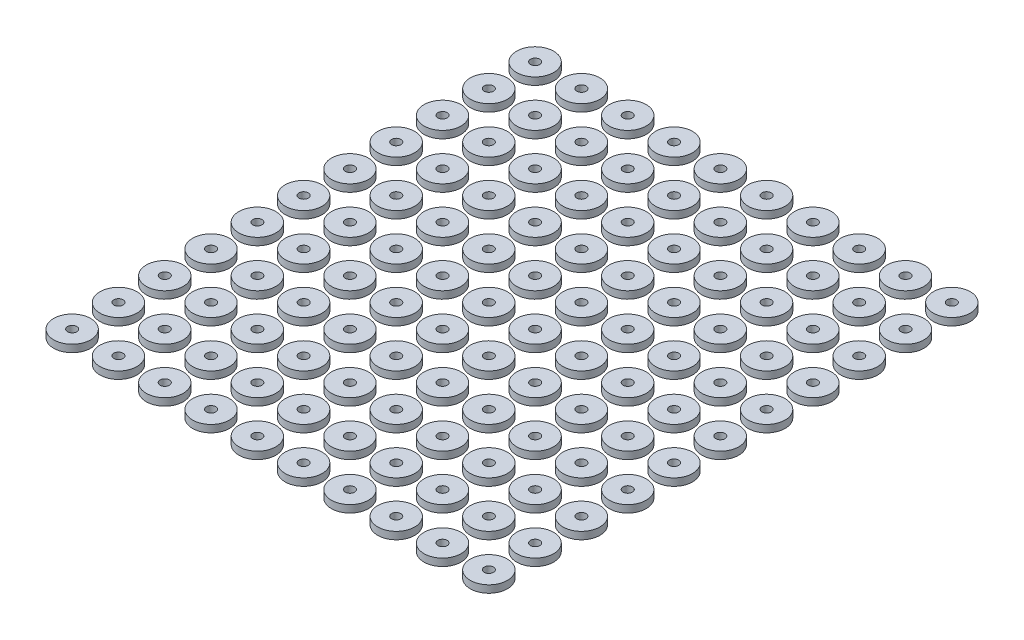
SolidWorks part; units mm, degrees
ref_plane "Front Plane" through (0, 0, 0) normal (0, 0, 1) x (1, 0, 0)
ref_plane "Top Plane" through (0, 0, 0) normal (0, 1, 0) x (1, 0, 0)
ref_plane "Right Plane" through (0, 0, 0) normal (1, 0, 0) x (0, 0, -1)
sketch "Sketch1" plane through (0, 0, 0) normal (0, 1, 0) x (1, 0, 0)
  circle A0 centre (0, 0) radius 4
  circle A110 centre (0, 0) radius 1
  circle A111 centre (10, 0) radius 4
  circle A112 centre (10, 0) radius 1
  circle A113 centre (20, 0) radius 4
  circle A114 centre (20, 0) radius 1
  circle A115 centre (30, 0) radius 4
  circle A116 centre (30, 0) radius 1
  circle A117 centre (40, 0) radius 4
  circle A118 centre (40, 0) radius 1
  circle A119 centre (50, 0) radius 4
  circle A120 centre (50, 0) radius 1
  circle A121 centre (60, 0) radius 4
  circle A122 centre (60, 0) radius 1
  circle A123 centre (70, 0) radius 4
  circle A124 centre (70, 0) radius 1
  circle A125 centre (80, 0) radius 4
  circle A126 centre (80, 0) radius 1
  circle A127 centre (90, 0) radius 4
  circle A128 centre (90, 0) radius 1
  circle A129 centre (10, 10) radius 4
  circle A130 centre (10, 10) radius 1
  circle A131 centre (20, 10) radius 4
  circle A132 centre (20, 10) radius 1
  circle A133 centre (30, 10) radius 4
  circle A134 centre (30, 10) radius 1
  circle A135 centre (40, 10) radius 4
  circle A136 centre (40, 10) radius 1
  circle A137 centre (50, 10) radius 4
  circle A138 centre (50, 10) radius 1
  circle A139 centre (60, 10) radius 4
  circle A140 centre (60, 10) radius 1
  circle A141 centre (70, 10) radius 4
  circle A142 centre (70, 10) radius 1
  circle A143 centre (80, 10) radius 4
  circle A144 centre (80, 10) radius 1
  circle A145 centre (90, 10) radius 4
  circle A146 centre (90, 10) radius 1
  circle A147 centre (10, 20) radius 4
  circle A148 centre (10, 20) radius 1
  circle A149 centre (20, 20) radius 4
  circle A150 centre (20, 20) radius 1
  circle A151 centre (30, 20) radius 4
  circle A152 centre (30, 20) radius 1
  circle A153 centre (40, 20) radius 4
  circle A154 centre (40, 20) radius 1
  circle A155 centre (50, 20) radius 4
  circle A156 centre (50, 20) radius 1
  circle A157 centre (60, 20) radius 4
  circle A158 centre (60, 20) radius 1
  circle A159 centre (70, 20) radius 4
  circle A160 centre (70, 20) radius 1
  circle A161 centre (80, 20) radius 4
  circle A162 centre (80, 20) radius 1
  circle A163 centre (90, 20) radius 4
  circle A164 centre (90, 20) radius 1
  circle A165 centre (10, 30) radius 4
  circle A166 centre (10, 30) radius 1
  circle A167 centre (20, 30) radius 4
  circle A168 centre (20, 30) radius 1
  circle A169 centre (30, 30) radius 4
  circle A170 centre (30, 30) radius 1
  circle A171 centre (40, 30) radius 4
  circle A172 centre (40, 30) radius 1
  circle A173 centre (50, 30) radius 4
  circle A174 centre (50, 30) radius 1
  circle A175 centre (60, 30) radius 4
  circle A176 centre (60, 30) radius 1
  circle A177 centre (70, 30) radius 4
  circle A178 centre (70, 30) radius 1
  circle A179 centre (80, 30) radius 4
  circle A180 centre (80, 30) radius 1
  circle A181 centre (90, 30) radius 4
  circle A182 centre (90, 30) radius 1
  circle A183 centre (10, 40) radius 4
  circle A184 centre (10, 40) radius 1
  circle A185 centre (20, 40) radius 4
  circle A186 centre (20, 40) radius 1
  circle A187 centre (30, 40) radius 4
  circle A188 centre (30, 40) radius 1
  circle A189 centre (40, 40) radius 4
  circle A190 centre (40, 40) radius 1
  circle A191 centre (50, 40) radius 4
  circle A192 centre (50, 40) radius 1
  circle A193 centre (60, 40) radius 4
  circle A194 centre (60, 40) radius 1
  circle A195 centre (70, 40) radius 4
  circle A196 centre (70, 40) radius 1
  circle A197 centre (80, 40) radius 4
  circle A198 centre (80, 40) radius 1
  circle A199 centre (90, 40) radius 4
  circle A200 centre (90, 40) radius 1
  circle A201 centre (10, 50) radius 4
  circle A202 centre (10, 50) radius 1
  circle A203 centre (20, 50) radius 4
  circle A204 centre (20, 50) radius 1
  circle A205 centre (30, 50) radius 4
  circle A206 centre (30, 50) radius 1
  circle A207 centre (40, 50) radius 4
  circle A208 centre (40, 50) radius 1
  circle A209 centre (50, 50) radius 4
  circle A210 centre (50, 50) radius 1
  circle A211 centre (60, 50) radius 4
  circle A212 centre (60, 50) radius 1
  circle A213 centre (70, 50) radius 4
  circle A214 centre (70, 50) radius 1
  circle A215 centre (80, 50) radius 4
  circle A216 centre (80, 50) radius 1
  circle A217 centre (90, 50) radius 4
  circle A218 centre (90, 50) radius 1
  circle A219 centre (10, 60) radius 4
  circle A220 centre (10, 60) radius 1
  circle A221 centre (20, 60) radius 4
  circle A222 centre (20, 60) radius 1
  circle A223 centre (30, 60) radius 4
  circle A224 centre (30, 60) radius 1
  circle A225 centre (40, 60) radius 4
  circle A226 centre (40, 60) radius 1
  circle A227 centre (50, 60) radius 4
  circle A228 centre (50, 60) radius 1
  circle A229 centre (60, 60) radius 4
  circle A230 centre (60, 60) radius 1
  circle A231 centre (70, 60) radius 4
  circle A232 centre (70, 60) radius 1
  circle A233 centre (80, 60) radius 4
  circle A234 centre (80, 60) radius 1
  circle A235 centre (90, 60) radius 4
  circle A236 centre (90, 60) radius 1
  circle A237 centre (10, 70) radius 4
  circle A238 centre (10, 70) radius 1
  circle A239 centre (20, 70) radius 4
  circle A240 centre (20, 70) radius 1
  circle A241 centre (30, 70) radius 4
  circle A242 centre (30, 70) radius 1
  circle A243 centre (40, 70) radius 4
  circle A244 centre (40, 70) radius 1
  circle A245 centre (50, 70) radius 4
  circle A246 centre (50, 70) radius 1
  circle A247 centre (60, 70) radius 4
  circle A248 centre (60, 70) radius 1
  circle A249 centre (70, 70) radius 4
  circle A250 centre (70, 70) radius 1
  circle A251 centre (80, 70) radius 4
  circle A252 centre (80, 70) radius 1
  circle A253 centre (90, 70) radius 4
  circle A254 centre (90, 70) radius 1
  circle A255 centre (10, 80) radius 4
  circle A256 centre (10, 80) radius 1
  circle A257 centre (20, 80) radius 4
  circle A258 centre (20, 80) radius 1
  circle A259 centre (30, 80) radius 4
  circle A260 centre (30, 80) radius 1
  circle A261 centre (40, 80) radius 4
  circle A262 centre (40, 80) radius 1
  circle A263 centre (50, 80) radius 4
  circle A264 centre (50, 80) radius 1
  circle A265 centre (60, 80) radius 4
  circle A266 centre (60, 80) radius 1
  circle A267 centre (70, 80) radius 4
  circle A268 centre (70, 80) radius 1
  circle A269 centre (80, 80) radius 4
  circle A270 centre (80, 80) radius 1
  circle A271 centre (90, 80) radius 4
  circle A272 centre (90, 80) radius 1
  circle A273 centre (10, 90) radius 4
  circle A274 centre (10, 90) radius 1
  circle A275 centre (20, 90) radius 4
  circle A276 centre (20, 90) radius 1
  circle A277 centre (30, 90) radius 4
  circle A278 centre (30, 90) radius 1
  circle A279 centre (40, 90) radius 4
  circle A280 centre (40, 90) radius 1
  circle A281 centre (50, 90) radius 4
  circle A282 centre (50, 90) radius 1
  circle A283 centre (60, 90) radius 4
  circle A284 centre (60, 90) radius 1
  circle A285 centre (70, 90) radius 4
  circle A286 centre (70, 90) radius 1
  circle A287 centre (80, 90) radius 4
  circle A288 centre (80, 90) radius 1
  circle A289 centre (90, 90) radius 4
  circle A290 centre (90, 90) radius 1
  circle A291 centre (10, 100) radius 4
  circle A292 centre (10, 100) radius 1
  circle A293 centre (20, 100) radius 4
  circle A294 centre (20, 100) radius 1
  circle A295 centre (30, 100) radius 4
  circle A296 centre (30, 100) radius 1
  circle A297 centre (40, 100) radius 4
  circle A298 centre (40, 100) radius 1
  circle A299 centre (50, 100) radius 4
  circle A300 centre (50, 100) radius 1
  circle A301 centre (60, 100) radius 4
  circle A302 centre (60, 100) radius 1
  circle A303 centre (70, 100) radius 4
  circle A304 centre (70, 100) radius 1
  circle A305 centre (80, 100) radius 4
  circle A306 centre (80, 100) radius 1
  circle A307 centre (90, 100) radius 4
  circle A308 centre (90, 100) radius 1
  circle A309 centre (0, 10) radius 4
  circle A310 centre (0, 10) radius 1
  circle A311 centre (0, 20) radius 4
  circle A312 centre (0, 20) radius 1
  circle A313 centre (0, 30) radius 4
  circle A314 centre (0, 30) radius 1
  circle A315 centre (0, 40) radius 4
  circle A316 centre (0, 40) radius 1
  circle A317 centre (0, 50) radius 4
  circle A318 centre (0, 50) radius 1
  circle A319 centre (0, 60) radius 4
  circle A320 centre (0, 60) radius 1
  circle A321 centre (0, 70) radius 4
  circle A322 centre (0, 70) radius 1
  circle A323 centre (0, 80) radius 4
  circle A324 centre (0, 80) radius 1
  circle A325 centre (0, 90) radius 4
  circle A326 centre (0, 90) radius 1
  circle A327 centre (0, 100) radius 4
  circle A328 centre (0, 100) radius 1
  dimension "D1" = 10
  dimension "D2" = 11
extrude "Boss-Extrude1" add sketch "Sketch1" along normal blind 1.5875
